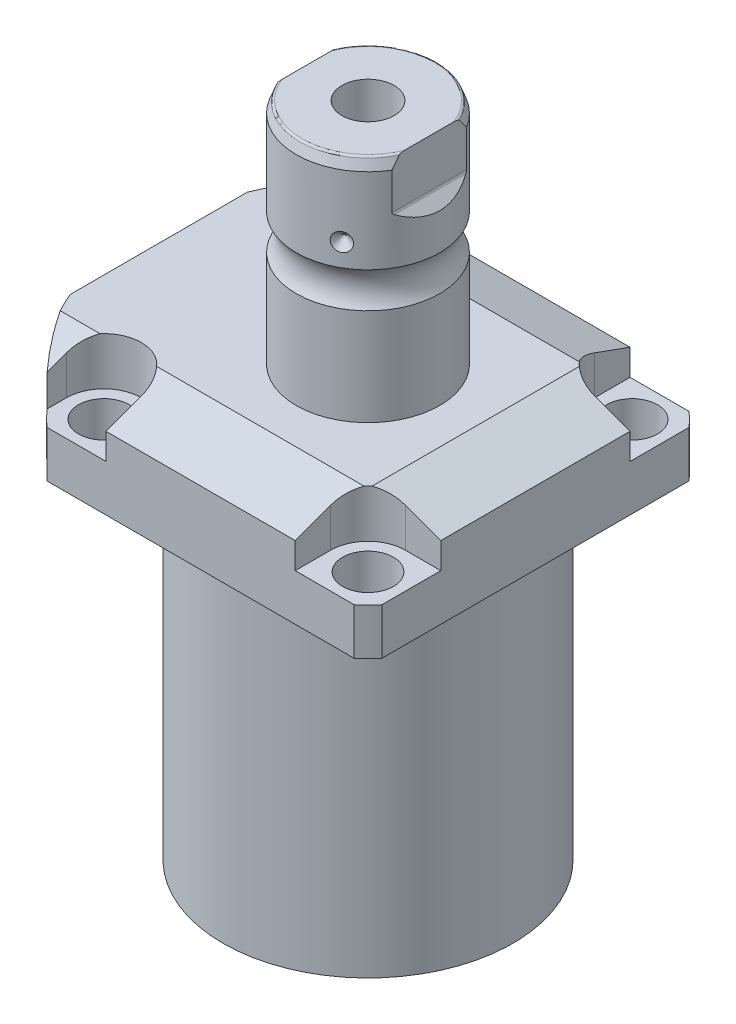
SolidWorks part; units mm, degrees
material "Alloy Steel"
ref_plane "Front Plane" through (0, 0, 0) normal (0, 0, 1) x (1, 0, 0)
ref_plane "Top Plane" through (0, 0, 0) normal (0, 1, 0) x (1, 0, 0)
ref_plane "Right Plane" through (0, 0, 0) normal (1, 0, 0) x (0, 0, -1)
ref_plane "Plane1" through (0, 0, 0) normal (0, 1, 0) x (0, 0, 1)
sketch "Sketch1" plane through (0, 0, 0) normal (0, 1, 0) x (0, 0, 1)
  line L0 (-44.45, 44.45) -> (44.45, 44.45)
  line L1 (44.45, 44.45) -> (44.45, -55.55)
  line L2 (44.45, -55.55) -> (-44.45, -55.55)
  line L3 (-44.45, -55.55) -> (-44.45, 44.45)
  line L4 (0, 0) -> (0, -60.6467) construction
  dimension "D1" = 55.55
  dimension "D2" = 100
  dimension "D3" = 88.9
extrude "Extrude1" add sketch "Sketch1" along normal blind 113.919
sketch "Sketch2" plane through (0, 0, 0) normal (0, -1, 0) x (1, 0, 0)
  circle A0 centre (0, 0) radius 60.325
  dimension "D1" = 120.65
extrude "Cut-Extrude1" cut sketch "Sketch2" against normal through all flip side to cut
ref_plane "Plane2" through (0, 0, 0) normal (1, 0, 0) x (0, 0, 1)
sketch "Sketch3" plane through (0, 0, 0) normal (1, 0, 0) x (0, 0, 1)
  line L0 (38.4935, 0) -> (38.4935, -88.9)
  line L1 (38.4935, -88.9) -> (76.5937, -88.9)
  line L2 (76.5937, -88.9) -> (76.5937, 0)
  line L3 (76.5937, 0) -> (38.4935, 0)
  line L4 (0, -93.345) -> (0, 4.445) construction
  line L5 (40.7836, 0) -> (-40.7836, 0) construction
  dimension "D1" = 76.987
  dimension "D2" = 153.1874
  dimension "D3" = 88.9
revolve "Cut-Revolve1" cut sketch "Sketch3" angle 360 about L4
fillet "Fillet1" radius 0.381 1 edges at (0, 88.9, 38.4935)
sketch "Sketch4" plane through (0, 113.919, 0) normal (0, 1, 0) x (-1, 0, 0)
  line L0 (-44.45, 40.7836) -> (-44.45, -40.7836) construction
  line L1 (40.7836, 44.45) -> (-40.7836, 44.45) construction
  line L2 (-25.121, -44.45) -> (-25.121, -35.052)
  line L3 (-44.45, -44.45) -> (-25.121, -44.45)
  line L4 (-44.45, -25.121) -> (-44.45, -44.45)
  line L5 (-35.052, -25.121) -> (-44.45, -25.121)
  line L6 (44.983, -44.45) -> (25.121, -44.45)
  line L7 (25.121, 44.45) -> (25.121, 35.052)
  line L8 (44.983, 44.45) -> (44.983, 35.052)
  line L9 (44.983, 44.45) -> (25.121, 44.45)
  line L10 (-35.052, 25.121) -> (-44.45, 25.121)
  line L11 (-44.45, 25.121) -> (-44.45, 44.45)
  line L12 (-44.45, 44.45) -> (-25.121, 44.45)
  line L13 (-25.121, 44.45) -> (-25.121, 35.052)
  line L14 (-48.9217, 0) -> (49.4551, 0) construction
  line L15 (44.983, -44.45) -> (44.983, -35.052)
  line L16 (25.121, -44.45) -> (25.121, -35.052)
  arc A0 (25.121, -35.052) -> (44.983, -35.052) centre (35.052, -35.052) cw
  arc A1 (-35.052, -25.121) -> (-25.121, -35.052) centre (-35.052, -35.052) cw
  arc A2 (-35.052, 25.121) -> (-25.121, 35.052) centre (-35.052, 35.052) ccw
  arc A3 (25.121, 35.052) -> (44.983, 35.052) centre (35.052, 35.052) ccw
  dimension "D2" = 9.931
  dimension "D1" = 35.052
  dimension "D3" = 35.052
  dimension "D4" = 35.052
extrude "Cut-Extrude2" cut sketch "Sketch4" against normal blind 12.7
ref_plane "Plane3" through (0, 0, 0) normal (1, 0, 0) x (0, 0, -1)
sketch "Sketch5" plane through (0, 0, 0) normal (1, 0, 0) x (0, 0, -1)
  line L0 (-28.575, 113.919) -> (-44.45, 108.141)
  line L1 (0, 0) -> (0, 154.1081) construction
  line L2 (-28.575, 113.919) -> (-44.45, 113.919)
  line L3 (-44.45, 113.919) -> (-44.45, 108.141)
  dimension "D1" = 15.875
  dimension "D2" = 20
extrude "Cut-Extrude9" cut sketch "Sketch5" against normal through all and the other way through all
mirror "Mirror1" about plane through (0, 0, 0) normal (0, 0, 1) of "Cut-Extrude9"
ref_plane "Plane7" through (0, 0, 0) normal (0, 0, 1) x (1, 0, 0)
sketch "Sketch9" plane through (0, 0, 0) normal (0, 0, 1) x (1, 0, 0)
  line L0 (28.575, 113.919) -> (44.45, 108.141)
  line L1 (44.45, 108.141) -> (44.45, 113.919)
  line L2 (44.45, 113.919) -> (28.575, 113.919)
  dimension "D1" = 15.875
  dimension "D2" = 20
extrude "Cut-Extrude7" cut sketch "Sketch9" against normal through all and the other way through all
ref_plane "Plane8" through (-41.402, 88.9, -18.1102) normal (1, 0, 0) x (0, 1, 0)
sketch "Sketch20" plane through (-41.402, 88.9, -18.1102) normal (1, 0, 0) x (0, 1, 0)
  line L0 (-88.9, 18.1102) -> (39.8401, 18.1102) construction
  line L1 (-7.2797, 36.2202) -> (36.9042, 36.2202) construction
  line L2 (0, 41.9225) -> (1.4478, 41.9225)
  line L3 (0, 58.8938) -> (0, -22.6734) construction
  line L4 (1.4478, 41.9225) -> (1.4478, 39.4714)
  line L5 (1.4478, 39.4714) -> (2.4638, 39.4714)
  line L6 (2.4638, 39.4714) -> (2.4638, 37.4648)
  line L7 (2.4638, 37.4648) -> (13.4366, 37.4648)
  line L8 (13.4366, 37.4648) -> (13.4366, 36.2202)
  line L9 (13.4366, 36.2202) -> (0, 36.2202)
  line L10 (0, 41.9225) -> (0, 36.2202)
  dimension "D1" = 18.11
  dimension "D2" = 11.4046
  dimension "D3" = 1.4478
  dimension "D4" = 6.5024
  dimension "D5" = 1.016
  dimension "D6" = 2.4892
  dimension "D7" = 10.9728
revolve "Cut-Revolve4" cut sketch "Sketch20" angle 360 about L1
mirror "Mirror10" about plane through (0, 0, 0) normal (0, 0, 1) of "Cut-Revolve4"
sketch "Sketch10" plane through (-41.402, 88.9, -18.1102) normal (1, 0, 0) x (0, 1, 0)
  line L0 (-1.0325, 0.0002) -> (1.5659, 0.0002) construction
  line L1 (13.4366, 1.2448) -> (2.4638, 1.2448) construction
  line L2 (2.4638, -1.2444) -> (13.4366, -1.2444) construction
  line L3 (0, 58.8938) -> (0, -22.6734) construction
  circle A0 centre (0.2667, 4.5214) radius 1.1811
  dimension "D1" = 2.3622
  dimension "D2" = 0.2667
  dimension "D3" = 9.0424
revolve "Revolve4" add sketch "Sketch10" angle 360 about L0
ref_plane "Plane9" through (-41.402, 88.9, 18.1102) normal (1, 0, 0) x (0, 1, 0)
sketch "Sketch11" plane through (-41.402, 88.9, 18.1102) normal (1, 0, 0) x (0, 1, 0)
  line L0 (-1.0325, -0.0002) -> (1.5659, -0.0002) construction
  line L1 (13.4366, 1.2444) -> (2.4638, 1.2444) construction
  line L3 (0, 22.6734) -> (0, -58.8938) construction
  line L4 (2.4638, -1.2448) -> (13.4366, -1.2448) construction
  circle A0 centre (0.2667, 4.521) radius 1.1811
  dimension "D1" = 2.3622
  dimension "D2" = 9.0424
  dimension "D3" = 0.2667
revolve "Revolve2" add sketch "Sketch11" angle 360 about L0
ref_plane "Plane10" through (-55.5498, 101.9048, 12.9794) normal (0, 0, 1) x (0, 1, 0)
sketch "S2D0007" plane through (-55.5498, 101.9048, 12.9794) normal (0, 0, 1) x (0, 1, 0)
  line L0 (0.0002, 0.0002) -> (10.7444, 0.0002)
  line L1 (10.7444, 0.0002) -> (10.7444, -0.2538)
  line L2 (10.7444, -0.2538) -> (6.655, -0.2538)
  line L3 (6.655, -0.2538) -> (5.9438, -0.965)
  line L5 (5.9438, -0.965) -> (5.9438, -14.427)
  line L6 (5.9438, -14.427) -> (0.0002, -14.427)
  line L7 (0.0002, -14.427) -> (0.0002, 0.0002)
  line L8 (0.0002, -14.9352) -> (0.0002, 0.7112) construction
  line L9 (-13.0048, 0.0002) -> (-13.0048, -14.7662) construction
  line L10 (12.0142, 0.0002) -> (-13.0048, 0.0002) construction
  dimension "D1" = 0.254
  dimension "D2" = 13.005
  dimension "D3" = 45
  dimension "D4" = 0.254
  dimension "D5" = 21.4884
  dimension "D6" = 13.3096
  dimension "D9" = 11.8872
  dimension "D10" = 14.1732
revolve "Cut-Revolve2" cut sketch "S2D0007" angle 360 about L8
pattern_linear "LPattern1" count 2 spacing 25.9588 along (0, 0, -1) of "Cut-Revolve2"
ref_plane "Plane12" through (0, 0, 0) normal (1, 0, 0) x (0, -1, 0)
sketch "Sketch15" plane through (0, 0, 0) normal (1, 0, 0) x (0, -1, 0)
  line L0 (-113.919, 0) -> (-113.919, 19.05)
  line L1 (-113.919, 19.05) -> (-139.6407, 19.05)
  line L2 (-149.0553, 19.05) -> (-171.602, 19.05)
  line L3 (-174.523, 17.9868) -> (-174.523, 0)
  line L4 (-174.523, 0) -> (-113.919, 0)
  line L5 (-197.6361, 0) -> (-64.6704, 0) construction
  line L6 (-113.919, 27.5238) -> (-113.919, -27.5238) construction
  line L8 (-174.523, 17.9868) -> (-171.602, 19.05)
  line L9 (0, -38.4935) -> (0, 38.4935) construction
  arc A0 (-149.0553, 19.05) -> (-139.6407, 19.05) centre (-144.348, 25.4255) ccw
  dimension "D2" = 20
  dimension "D4" = 7.925
  dimension "D6" = 35.001
  dimension "D1" = 174.523
  dimension "D3" = 38.1
  dimension "D5" = 30.175
  dimension "D7" = 2.921
revolve "Revolve3" add sketch "Sketch15" angle 360 about L5
ref_plane "Plane13" through (0, 0, 0) normal (0, 0, -1) x (0, -1, 0)
sketch "Sketch16" plane through (0, 0, 0) normal (0, 0, 1) x (0, -1, 0)
  line L0 (-174.523, 19.05) -> (-158.7384, 19.05)
  line L1 (-174.523, -19.05) -> (-174.523, -16.281)
  line L2 (-174.523, 16.281) -> (-161.823, 16.281)
  line L3 (-161.2842, 16.5042) -> (-158.7384, 19.05)
  line L4 (-161.2842, -16.5042) -> (-158.7384, -19.05)
  line L5 (-174.523, -16.281) -> (-161.823, -16.281)
  line L6 (-174.523, 19.05) -> (-174.523, 16.281)
  line L7 (-174.523, -19.05) -> (-158.7384, -19.05)
  line L8 (-194.0458, 0) -> (-125.0021, 0) construction
  line L11 (-174.523, 17.9868) -> (-174.523, -17.9868) construction
  line L12 (-149.0553, 19.05) -> (-171.602, 19.05) construction
  arc A0 (-161.823, 16.281) -> (-161.2842, 16.5042) centre (-161.823, 17.043) ccw
  arc A1 (-161.823, -16.281) -> (-161.2842, -16.5042) centre (-161.823, -17.043) cw
  point P3 (-161.5074, 16.281)
  dimension "D4" = 0.762
  dimension "D1" = 32.562
  dimension "D2" = 45
  dimension "D3" = 12.7
extrude "Cut-Extrude8" cut sketch "Sketch16" against normal mid plane 106.68
hole_wizard "Hole1" positions "Sketch18" profile "Sketch17" legacy end condition up to next
sketch "Sketch18" plane through (0, 101.219, 0) normal (0, 1, 0) x (-1, 0, 0)
  arc A0 (44.983, -35.052) -> (25.121, -35.052) centre (35.052, -35.052) ccw construction
  arc A1 (25.121, 35.052) -> (44.983, 35.052) centre (35.052, 35.052) ccw construction
  arc A2 (-35.052, 25.121) -> (-25.121, 35.052) centre (-35.052, 35.052) ccw construction
  arc A3 (-25.121, -35.052) -> (-35.052, -25.121) centre (-35.052, -35.052) ccw construction
  point P0 (-35.052, -35.052)
  point P1 (-35.052, 35.052)
  point P3 (35.052, 35.052)
  point P5 (35.052, -35.052)
sketch "Sketch17" plane through (35.052, 101.219, -35.052) normal (1, 0, 0) x (0, 0, 1)
  line L0 (0, 0) -> (0, 12.319)
  line L1 (0, 12.319) -> (6.7435, 12.319)
  line L2 (6.7435, 12.319) -> (6.7435, 0)
  line L3 (6.7435, 0) -> (0, 0)
  line L4 (0, 110) -> (0, -10) construction
  dimension "Diameter" = 13.487
  dimension "Depth" = 12.319
chamfer "Chamfer1" distance 0.635 angle 45 2 edges at (-41.402, 91.3638, 16.8654) (-41.402, 91.3638, -16.8654)
sketch "Sketch21" plane through (0, 0, 0) normal (0, 0, 1) x (1, 0, 0)
  line L0 (0, 0) -> (0, 194.0957) construction
  line L1 (0, 144.9565) -> (6.9342, 149.123)
  line L2 (6.9342, 149.123) -> (6.9342, 174.523)
  line L4 (6.9342, 174.523) -> (0, 174.523)
  line L5 (0, 174.523) -> (0, 144.9565)
  line L6 (16.281, 174.523) -> (-16.281, 174.523) construction
  dimension "D1" = 13.8684
  dimension "D2" = 59
  dimension "D3" = 25.4
revolve "Cut-Revolve5" cut sketch "Sketch21" angle 360 about L0
fillet "Fillet2" radius 0.635 2 edges at (0, 174.523, -17.9868) (0, 174.523, 17.9868)
sketch "Sketch22" plane through (0, 0, 0) normal (0, 0, 1) x (1, 0, 0)
  line L0 (-37.9974, 155.016) -> (37.12, 155.016) construction
  line L1 (-19.05, 157.429) -> (-16.637, 155.016)
  line L2 (-16.637, 155.016) -> (-19.05, 155.016)
  line L3 (-19.05, 155.016) -> (-19.05, 157.429)
  arc A0 (-19.05, 139.6407) -> (-19.05, 149.0553) centre (-25.4255, 144.348) ccw construction
  dimension "D2" = 10.668
  dimension "D1" = 4.826
  dimension "D3" = 45
revolve "Cut-Revolve6" cut sketch "Sketch22" angle 360 about L0
pattern_circular "CirPattern1" count 3 over 360 about axis through (0, 197.6361, 0) along (0, 1, 0) of "Cut-Revolve6"
